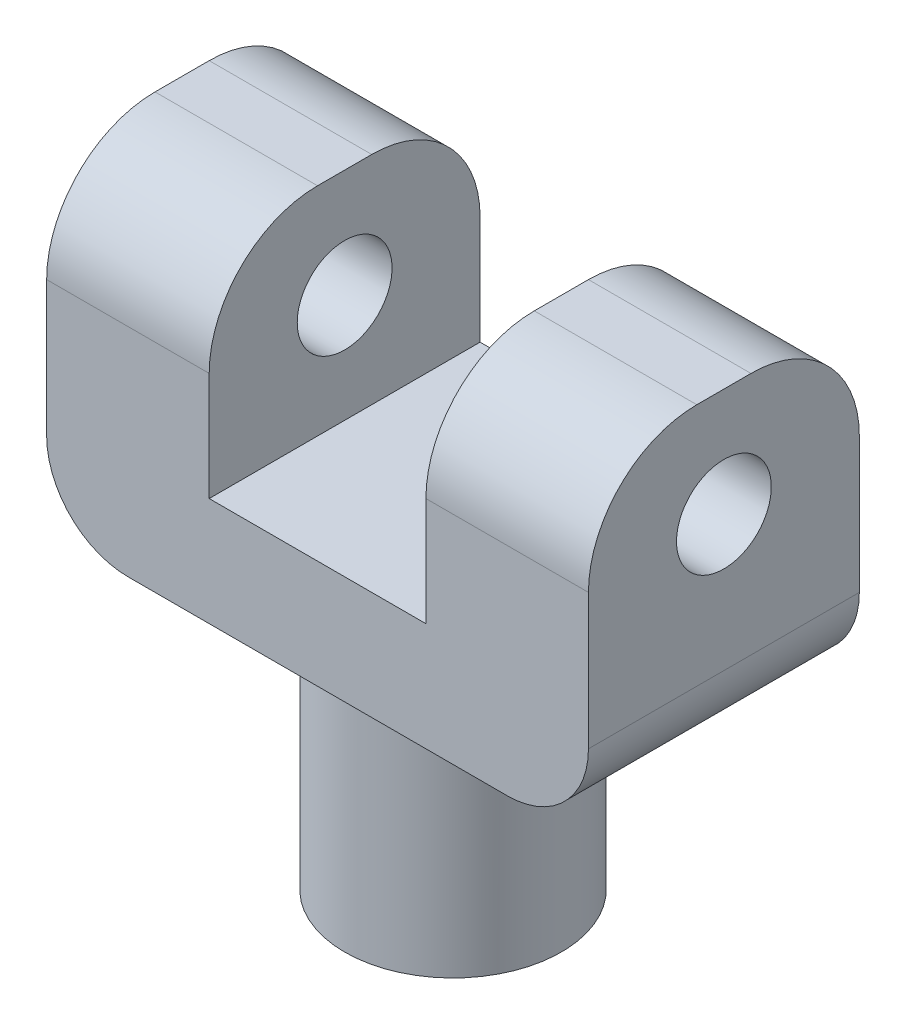
SolidWorks part; units mm, degrees
ref_plane "Front Plane" through (0, 0, 0) normal (0, 0, 1) x (1, 0, 0)
ref_plane "Top Plane" through (0, 0, 0) normal (0, 1, 0) x (1, 0, 0)
ref_plane "Right Plane" through (0, 0, 0) normal (1, 0, 0) x (0, 0, -1)
sketch "Sketch1" plane through (0, 0, 0) normal (0, 1, 0) x (1, 0, 0)
  line L1 (-10, 5) -> (10, 5)
  line L2 (-10, 5) -> (-10, -5)
  line L3 (-10, -5) -> (10, -5)
  line L4 (10, 5) -> (10, -5)
  line L5 (-10, 5) -> (10, -5) construction
  line L6 (-10, -5) -> (10, 5) construction
  point P0 (0, 0)
  dimension "D1" = 20
  dimension "D2" = 10
extrude "Boss-Extrude1" add sketch "Sketch1" along normal blind 12
sketch "Sketch2" plane through (0, 12, 0) normal (0, 1, 0) x (1, 0, 0)
  line L0 (10, 5) -> (-10, 5) construction
  line L1 (-4, 5) -> (4, 5)
  line L2 (-4, 5) -> (-4, -5)
  line L3 (-4, -5) -> (4, -5)
  line L4 (4, 5) -> (4, -5)
  line L5 (-10, -5) -> (10, -5) construction
  line L7 (0, 0) -> (0, -5) construction
  dimension "D2" = 8
extrude "Cut-Extrude1" cut sketch "Sketch2" against normal blind 8
fillet "Fillet1" radius 4 4 edges at (7, 12, 5) (7, 12, -5) (-7, 12, -5) (-7, 12, 5)
sketch "Sketch3" plane through (-10, 0, 0) normal (-1, 0, 0) x (0, 0, 1)
  line L0 (0, 12) -> (0, 8) construction
  line L1 (-1, 12) -> (1, 12) construction
  circle A0 centre (0, 8) radius 1.75
  point P7 (0, 0)
  dimension "D2" = 3.5
  dimension "D1" = 4
extrude "Cut-Extrude2" cut sketch "Sketch3" against normal through all
fillet "Fillet2" radius 3 2 edges at (-10, 0, 0) (10, 0, 0)
sketch "Sketch5" plane through (0, 0, 0) normal (0, -1, 0) x (1, 0, 0)
  circle A0 centre (0, 0) radius 4
  dimension "D1" = 8
extrude "Boss-Extrude2" add sketch "Sketch5" along normal blind 9
sketch "Sketch6" plane through (0, -9, 0) normal (0, -1, 0) x (1, 0, 0)
  circle A0 centre (0, 0) radius 2
extrude "Cut-Extrude3" cut sketch "Sketch6" against normal blind 7
